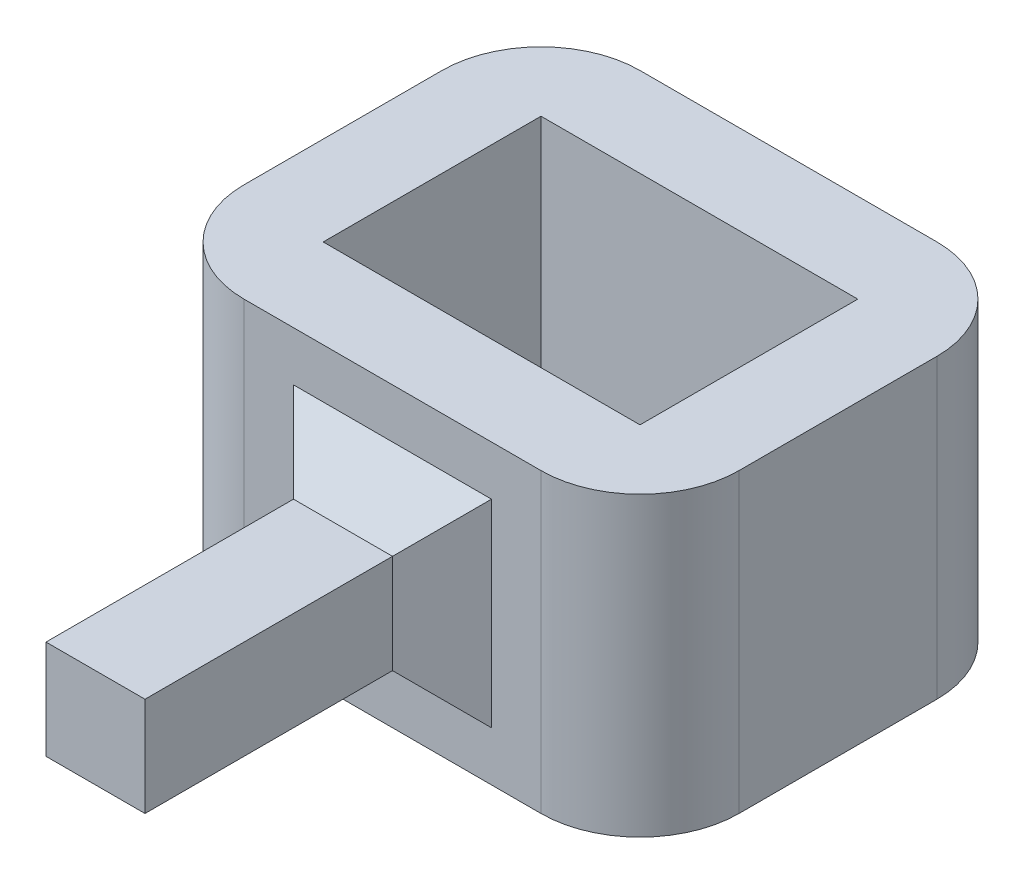
SolidWorks part; units mm, degrees
ref_plane "Front Plane" through (0, 0, 0) normal (0, 0, 1) x (1, 0, 0)
ref_plane "Top Plane" through (0, 0, 0) normal (0, 1, 0) x (1, 0, 0)
ref_plane "Right Plane" through (0, 0, 0) normal (1, 0, 0) x (0, 0, -1)
sketch "Sketch1" plane through (0, 0, 0) normal (0, 1, 0) x (1, 0, 0)
  line L0 (-14.1295, 3.1391) -> (-14.1295, -18.8609)
  line L1 (26.8705, 12.1391) -> (-23.1295, 12.1391)
  line L2 (26.8705, 12.1391) -> (26.8705, -27.8609)
  line L3 (26.8705, -27.8609) -> (-23.1295, -27.8609)
  line L4 (-23.1295, 12.1391) -> (-23.1295, -27.8609)
  line L5 (17.8705, -18.8609) -> (-14.1295, -18.8609)
  line L6 (17.8705, 3.1391) -> (17.8705, -18.8609)
  line L7 (17.8705, 3.1391) -> (-14.1295, 3.1391)
  dimension "D1" = 50
  dimension "D2" = 40
  dimension "D3" = 9
extrude "Boss-Extrude1" add sketch "Sketch1" along normal blind 30
sketch "Sketch2" plane through (0, 0, 27.8609) normal (0, 0, 1) x (1, 0, 0)
  line L0 (1.8705, 30) -> (1.8705, 0) construction
  line L1 (-23.1295, 0) -> (26.8705, 0)
  line L2 (-23.1295, 0) -> (-23.1295, 30)
  line L3 (-23.1295, 30) -> (26.8705, 30)
  line L4 (26.8705, 0) -> (26.8705, 30)
  line L5 (1.8705, 0) -> (1.8705, 15) construction
  line L7 (-3.1295, 10) -> (6.8705, 10)
  line L8 (-3.1295, 10) -> (-3.1295, 20)
  line L9 (-3.1295, 20) -> (6.8705, 20)
  line L10 (6.8705, 10) -> (6.8705, 20)
  line L11 (-3.1295, 10) -> (6.8705, 20) construction
  line L12 (-3.1295, 20) -> (6.8705, 10) construction
  dimension "D1" = 10
  dimension "D2" = 10
extrude "Boss-Extrude2" add sketch "Sketch2" along normal blind 30 contours L7 L10 L9 L8
chamfer "Chamfer1" distance 5 angle 45 4 edges at (1.8705, 20, 27.8609) (-3.1295, 15, 27.8609) (1.8705, 10, 27.8609) (6.8705, 15, 27.8609)
fillet "Fillet1" radius 10 4 edges at (-23.1295, 15, -12.1391) (26.8705, 15, -12.1391) (26.8705, 15, 27.8609) (-23.1295, 15, 27.8609)
